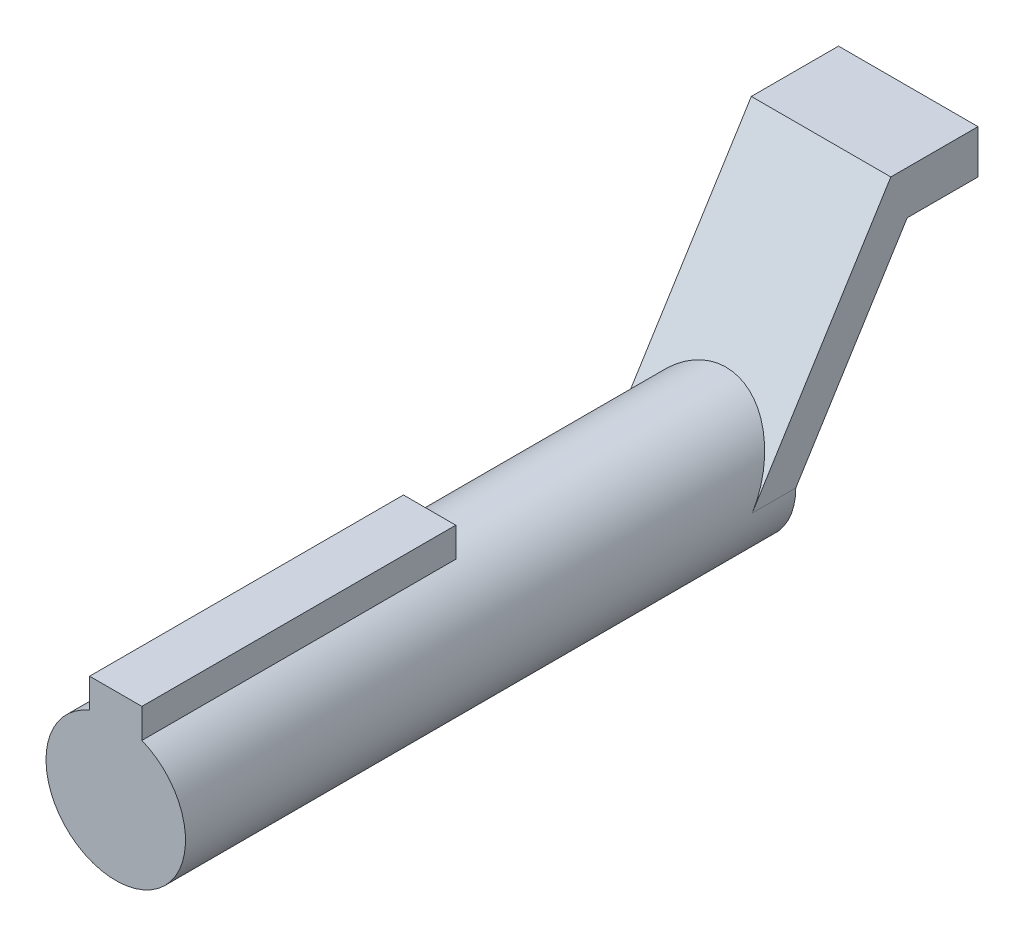
SolidWorks part; units mm, degrees
ref_plane "Front Plane" through (0, 0, 0) normal (0, 0, 1) x (1, 0, 0)
ref_plane "Top Plane" through (0, 0, 0) normal (0, 1, 0) x (1, 0, 0)
ref_plane "Right Plane" through (0, 0, 0) normal (1, 0, 0) x (0, 0, -1)
sketch "Sketch1" plane through (0, 0, 0) normal (0, 0, 1) x (1, 0, 0)
  circle A0 centre (0, 0) radius 4
  dimension "D1" = 8
extrude "Boss-Extrude1" add sketch "Sketch1" along normal blind 35
ref_plane "Plane1" through (4, 0, 0) normal (1, 0, 0) x (0, 0, -1)
ref_plane "Plane2" through (-4, 0, 0) normal (-1, 0, 0) x (0, 0, 1)
sketch "Sketch2" plane through (0, 0, 0) normal (1, 0, 0) x (0, 0, -1)
  line L0 (-2.5, 0) -> (0, 0)
  line L1 (-2.5, 0) -> (5.45, 12.72)
  line L2 (0, 0) -> (6.3875, 10.22)
  line L3 (5.45, 12.72) -> (7.95, 12.72)
  line L5 (5.45, 12.72) -> (10.45, 12.72)
  line L7 (6.3875, 10.22) -> (10.45, 10.22)
  line L8 (10.45, 12.72) -> (10.45, 10.22)
  dimension "D1" = 15
  dimension "D2" = 2.5
  dimension "D4" = 5
extrude "Boss-Extrude2" add sketch "Sketch2" along normal up to surface (4 mm away) and the other way up to surface (4 mm away) contours L8 L5 L3 L1 L0 L2 L7 up to plane "Plane1" other way up to plane "Plane2"
sketch "Sketch4" plane through (0, 0, 35) normal (0, 0, 1) x (1, 0, 0)
  line L1 (-1.5, 0) -> (1.5, 0)
  line L2 (-1.5, 0) -> (-1.5, 5.4)
  line L3 (-1.5, 5.4) -> (1.5, 5.4)
  line L4 (1.5, 0) -> (1.5, 5.4)
  point P4 (-1.37, 0.844)
  point P5 (0, 0)
  point P6 (-1.5, 5.4)
  point P8 (1.5, 5.4)
extrude "Boss-Extrude3" add sketch "Sketch4" against normal blind 18 contours L3 L4 L1 L2
